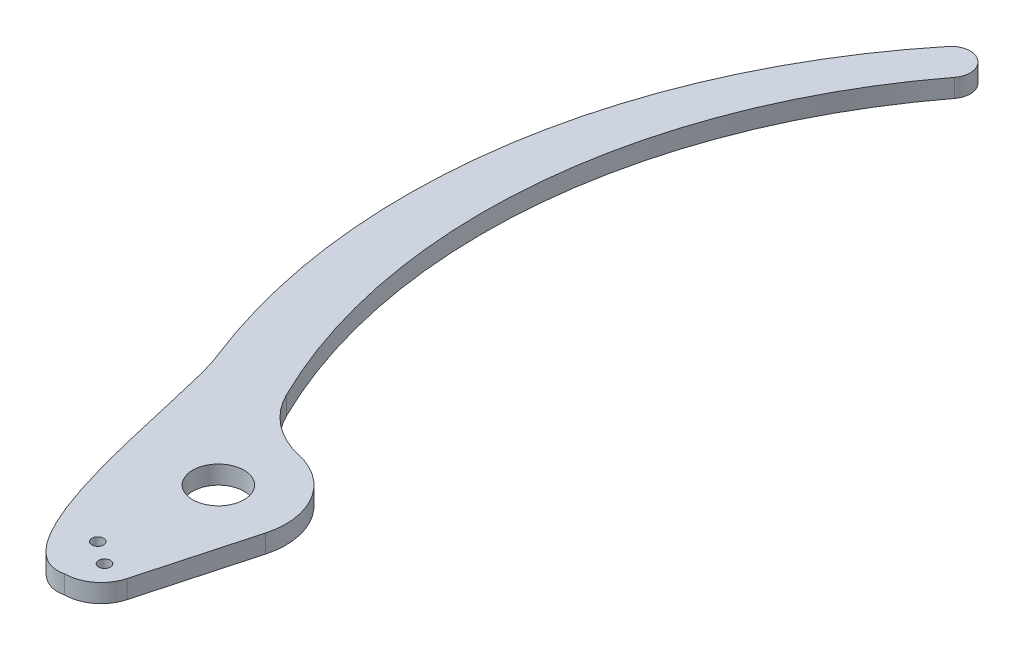
SolidWorks part; units mm, degrees
ref_plane "Front Plane" through (0, 0, 0) normal (0, 0, 1) x (1, 0, 0)
ref_plane "Top Plane" through (0, 0, 0) normal (0, 1, 0) x (1, 0, 0)
ref_plane "Right Plane" through (0, 0, 0) normal (1, 0, 0) x (0, 0, -1)
ref_plane "Plane1" through (0, -3.175, 0) normal (0, -1, 0) x (1, 0, 0)
sketch "Sketch1" plane through (0, -3.175, 0) normal (0, -1, 0) x (1, 0, 0)
  line L0 (11.303, 3.0969) -> (6.1243, 21.998)
  arc A0 (-19.5342, -19.4117) -> (-2.5602, -129.0853) centre (82.55, -59.7626) ccw
  arc A1 (-2.5602, -129.0853) -> (2.6242, -124.9958) centre (0, -127) ccw
  arc A2 (2.6242, -124.9958) -> (-7.62, -19.4117) centre (82.55, -63.9521) cw
  arc A3 (-7.62, -19.4117) -> (2.54, -11.441) centre (5.7789, -26.0303) cw
  arc A4 (2.54, -11.441) -> (11.303, 3.0969) centre (0, 0) ccw
  arc A5 (6.1243, 21.998) -> (0, 26.67) centre (0, 20.32) ccw
  circle A6 centre (0, 0) radius 4.445
  circle A7 centre (-1.9506, 18.9542) radius 1.016
  circle A8 centre (1.9506, 21.6858) radius 1.016
  spline S0 degree 3 poles (0, 26.67) (-11.2454, 29.3829) (-15.9815, -11.1104) (-19.5342, -19.4117) knots 0 0 0 0 1 1 1 1
extrude "Boss-Extrude1" add sketch "Sketch1" against normal blind 3.175
